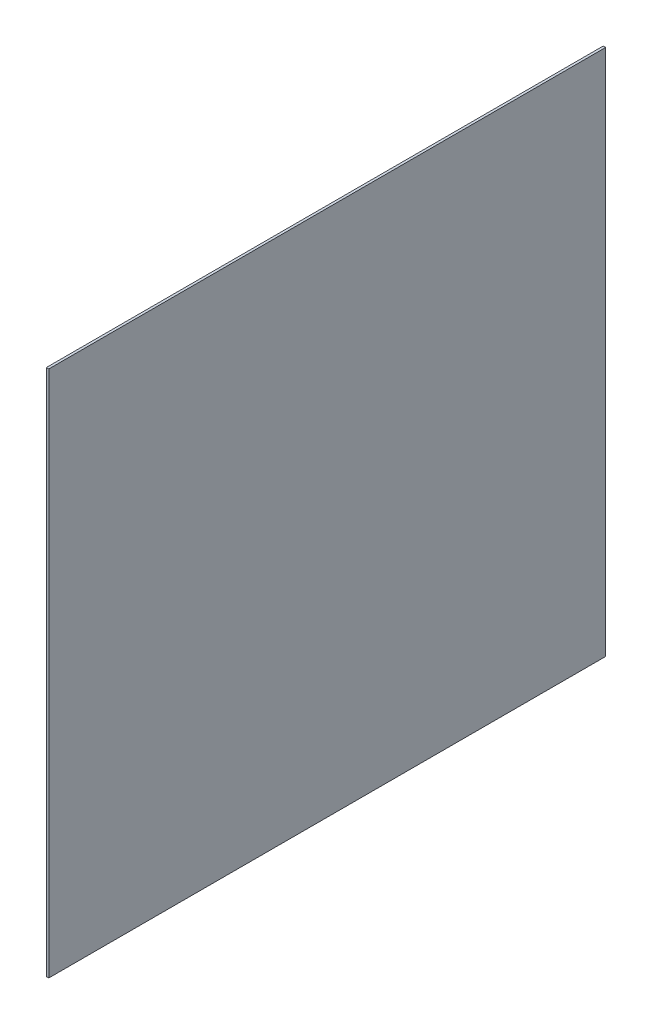
SolidWorks part; units mm, degrees
ref_plane "Front" through (0, 0, 0) normal (0, 0, 1) x (1, 0, 0)
ref_plane "Top" through (0, 0, 0) normal (0, 1, 0) x (1, 0, 0)
ref_plane "Right" through (0, 0, 0) normal (1, 0, 0) x (0, 0, -1)
sketch "Sketch1" plane through (0, 0, 0) normal (1, 0, 0) x (0, 0, -1)
  line L1 (-345.2421, 205.7567) -> (108.7579, 205.7567)
  line L2 (-345.2421, 205.7567) -> (-345.2421, -224.2433)
  line L3 (-345.2421, -224.2433) -> (108.7579, -224.2433)
  line L4 (108.7579, 205.7567) -> (108.7579, -224.2433)
  dimension "D1" = 454
  dimension "D2" = 430
extrude "Boss-Extrude1" add sketch "Sketch1" along normal blind 2
